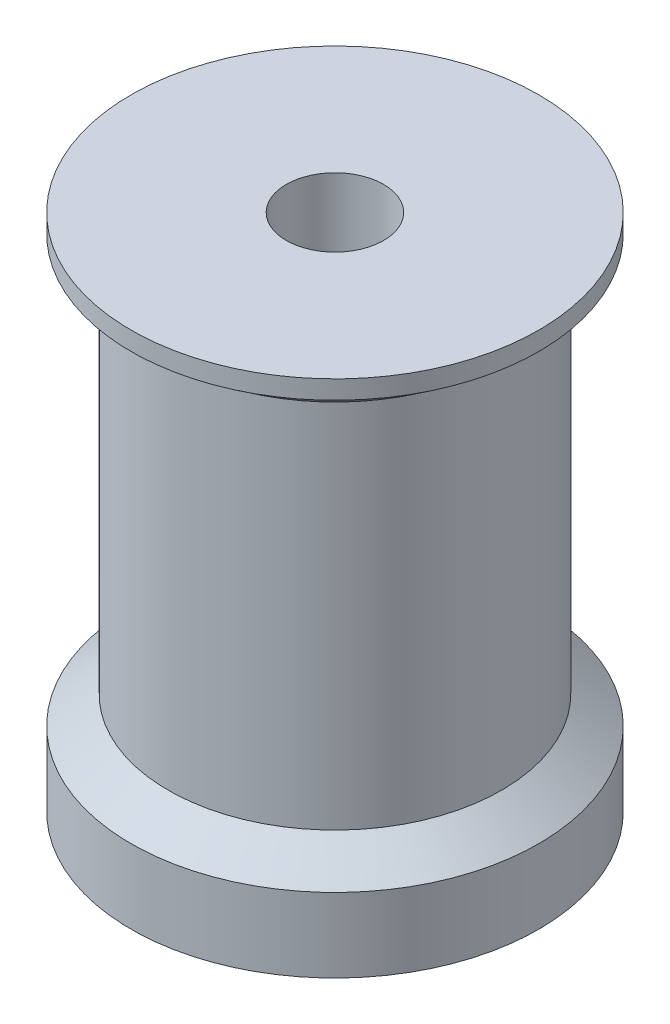
SolidWorks part; units mm, degrees
ref_plane "Front Plane" through (0, 0, 0) normal (0, 0, 1) x (1, 0, 0)
ref_plane "Top Plane" through (0, 0, 0) normal (0, 1, 0) x (1, 0, 0)
ref_plane "Right Plane" through (0, 0, 0) normal (1, 0, 0) x (0, 0, -1)
sketch "Sketch1" plane through (0, 0, 0) normal (0, 0, 1) x (1, 0, 0)
  line L0 (-2.625, 0) -> (-2.625, 28)
  line L1 (-2.625, 28) -> (-11, 28)
  line L2 (-11, 28) -> (-11, 27)
  line L3 (-11, 27) -> (-9, 25.5)
  line L4 (-9, 25.5) -> (-9, 5.5)
  line L5 (-9, 5.5) -> (-11, 4)
  line L6 (-11, 4) -> (-11, 0)
  line L7 (-11, 0) -> (-2.625, 0)
  line L8 (0, 0) -> (0, 18.0063) construction
  dimension "D1" = 5.25
  dimension "D2" = 28
  dimension "D3" = 9
  dimension "D4" = 11
  dimension "D5" = 1
  dimension "D6" = 2.5
  dimension "D7" = 4
  dimension "D8" = 5.5
revolve "Revolve1" add sketch "Sketch1" angle 360 about L8
